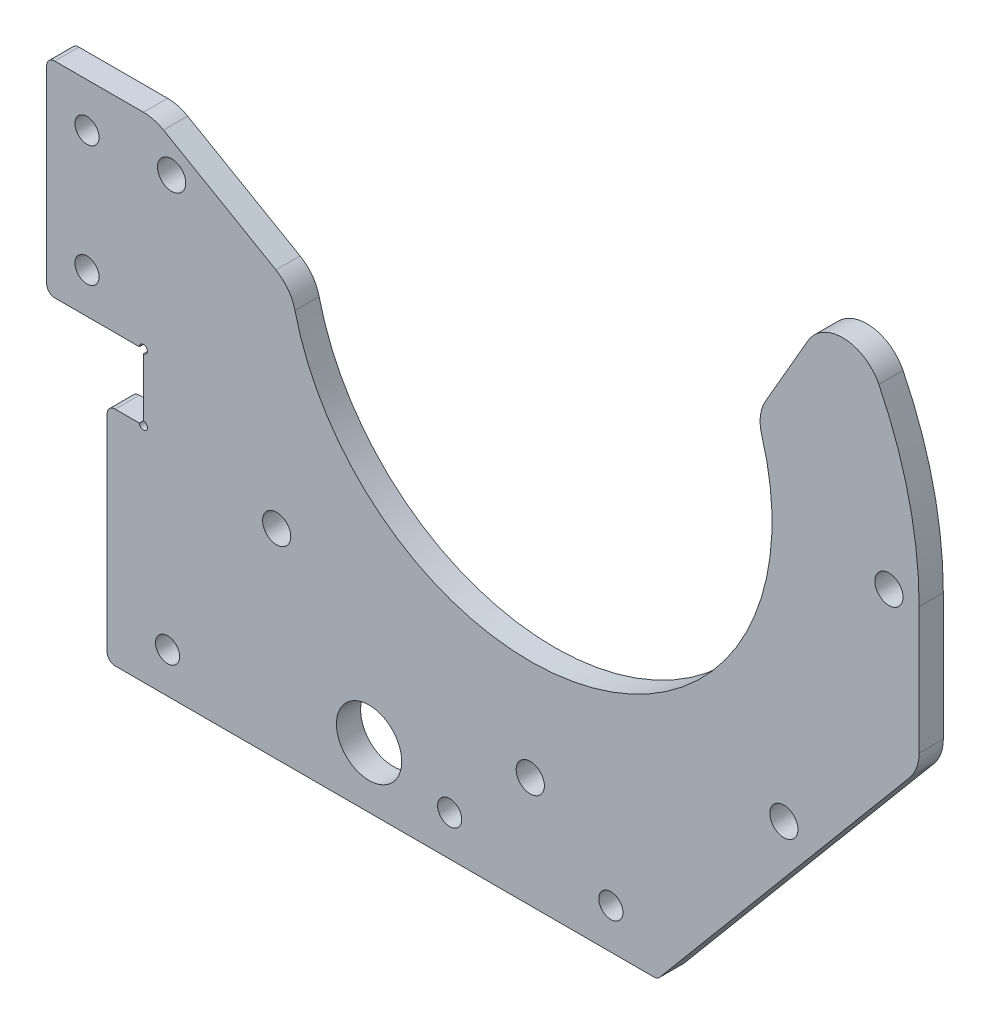
SolidWorks part; units mm, degrees
material "环氧板3240"
ref_plane "前视基准面" through (0, 0, 0) normal (0, 0, 1) x (1, 0, 0)
ref_plane "上视基准面" through (0, 0, 0) normal (0, 1, 0) x (1, 0, 0)
ref_plane "右视基准面" through (0, 0, 0) normal (1, 0, 0) x (0, 0, -1)
other "Configuration Table"
sketch "草图1" plane through (0, 0, 0) normal (0, 0, 1) x (1, 0, 0)
  line L0 (0, 0) -> (0, -44.5) construction
  line L1 (0, 0) -> (-31.4663, -31.4663) construction
  line L3 (48.25, 0) -> (48.25, -17.5616)
  line L4 (15.7865, -56.25) -> (-29.606, -56.25)
  line L5 (-29.606, -56.25) -> (-29.606, -4.8463) construction
  line L7 (-13.1909, -42.5) -> (13.1909, -42.5) construction
  line L8 (-13.7477, -46.25) -> (13.7477, -46.25) construction
  line L9 (-29.606, -56.25) -> (-60, -56.25)
  line L10 (-60, -56.25) -> (-60, 12.7017) construction
  line L11 (-60, 12.7017) -> (-29.606, -4.8463)
  line L12 (-60, -51.25) -> (19.982, -51.25) construction
  line L13 (-55, 9.815) -> (-55, -56.25) construction
  line L14 (-13.7477, 46.25) -> (13.7477, 46.25) construction
  line L15 (-44.5, 0) -> (44.5, 0) construction
  line L16 (-60, -20.45) -> (-48, -20.45)
  line L17 (-48, -20.45) -> (-48, -28.65)
  line L18 (-48, -28.65) -> (-60, -28.65)
  line L19 (0, -44.5) -> (0, -56.25) construction
  line L20 (15.7865, -56.25) -> (48.25, -17.5616)
  line L21 (-52.5, -28.65) -> (-52.5, -56.25)
  line L22 (-60, -20.45) -> (-60, 12.7017)
  line L23 (-60, 5) -> (-46.6603, 5)
  line L24 (28.0627, 10.606) -> (38.6303, 28.9096)
  line L25 (0, 0) -> (39.0494, 67.6355) construction
  line L26 (39.0494, 67.6355) -> (55.5038, 58.1355) construction
  line L27 (55.5038, 58.1355) -> (32.919, 19.0173) construction
  line L28 (32.919, 19.0173) -> (0.01, 38.0173) construction
  line L29 (0.01, 38.0173) -> (22.5949, 77.1355) construction
  line L30 (22.5949, 77.1355) -> (39.0494, 67.6355) construction
  line L31 (0, 0) -> (-65.5244, 37.8305) construction
  line L32 (-75.0244, 21.376) -> (-56.0244, 54.285) construction
  line L33 (-56.0244, 54.285) -> (-22.2268, 34.772) construction
  line L34 (-22.2268, 34.772) -> (-41.2268, 1.863) construction
  line L35 (-41.2268, 1.863) -> (-75.0244, 21.376) construction
  arc A0 (-29.606, -4.8463) -> (28.0627, 10.606) centre (0, 0) ccw
  circle A1 centre (0, 0) radius 44.5 construction
  circle A2 centre (-31.4663, -31.4663) radius 1.75
  circle A3 centre (0, -44.5) radius 1.75 construction
  circle A4 centre (31.4663, -31.4663) radius 1.75
  circle A5 centre (0, -42.5) radius 1.75
  circle A6 centre (0, 0) radius 48.25 construction
  circle A7 centre (-44.5, 0) radius 1.75
  circle A8 centre (44.5, 0) radius 1.75
  circle A9 centre (-10, -51.25) radius 1.5
  circle A10 centre (10, -51.25) radius 1.5
  circle A11 centre (-45, -51.25) radius 1.5
  circle A12 centre (-55, -15.45) radius 1.5
  circle A13 centre (-55, -0.45) radius 1.5
  arc A14 (48.25, 0) -> (38.6303, 28.9096) centre (0, 0) ccw
  point P64 (-65.5244, 37.8305)
  dimension "D2" = 89
  dimension "D3" = 60
  dimension "D4" = 3.5
  dimension "D6" = 42.5
  dimension "D8" = 96.5
  dimension "D12" = 3
  dimension "D13" = 5
  dimension "D14" = 35
  dimension "D19" = 10
  dimension "D21" = 20
  dimension "D22" = 38
  dimension "D23" = 7.5
  dimension "D24" = 15
  dimension "D1" = 45
  dimension "D5" = 60
  dimension "D7" = 5
  dimension "D9" = 92.5
  dimension "D10" = 10
  dimension "D11" = 5
  dimension "D15" = 27.6
  dimension "D16" = 8.2
  dimension "D17" = 12
  dimension "D18" = 60
  dimension "D20" = 50
  dimension "D25" = 60
  dimension "D26" = 38
  dimension "D27" = 30
  dimension "D28" = 30
  dimension "D29" = 61.25
extrude "凸台-拉伸1" add sketch "草图1" along normal blind 3
fillet "圆角1" radius 5 5 edges at (28.0627, 10.606, 1.5) (48.25, -17.5616, 1.5) (38.6303, 28.9096, 1.5) (-29.606, -4.8463, 1.5) (-46.6603, 5, 1.5)
sketch "草图3" plane through (0, 0, 0) normal (0, 0, -1) x (-1, 0, 0)
  circle A0 centre (48, -20.45) radius 0.5
  circle A1 centre (48, -28.65) radius 0.5
  dimension "D1" = 1
extrude "切除-拉伸1" cut sketch "草图3" against normal blind 10
sketch "草图4" plane through (0, 0, 3) normal (0, 0, 1) x (1, 0, 0)
  line L0 (15.7865, -56.25) -> (-52.5, -56.25) construction
  line L1 (-52.5, -28.65) -> (-52.5, -56.25) construction
  circle A0 centre (-20, -48.75) radius 4.05
  dimension "D1" = 8.1
  dimension "D2" = 7.5
  dimension "D3" = 32.5
extrude "切除-拉伸2" cut sketch "草图4" against normal blind 10
fillet "圆角2" radius 1 5 edges at (15.7865, -56.25, 1.5) (-60, 5, 1.5) (-52.5, -56.25, 1.5) (-52.5, -28.65, 1.5) (-60, -20.45, 1.5)
